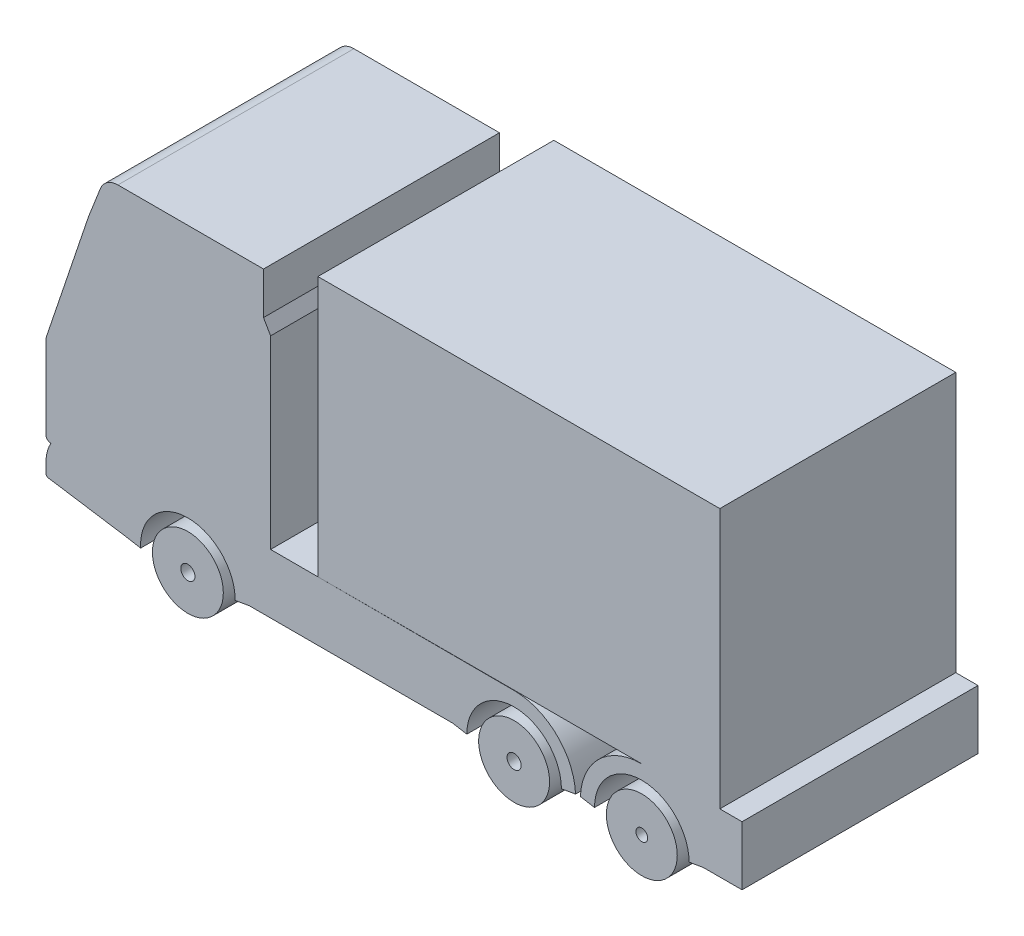
SolidWorks part; units mm, degrees
ref_plane "Front Plane" through (0, 0, 0) normal (0, 0, 1) x (1, 0, 0)
ref_plane "Top Plane" through (0, 0, 0) normal (0, 1, 0) x (1, 0, 0)
ref_plane "Right Plane" through (0, 0, 0) normal (1, 0, 0) x (0, 0, -1)
sketch "Sketch1" plane through (0, 0, 0) normal (0, 0, 1) x (1, 0, 0)
  line L0 (1512.2242, 1030.7259) -> (1489.9408, 1030.763)
  line L1 (0, 538.3532) -> (0, 642.5001)
  line L2 (6300, 1028.4561) -> (7360, 1028.4561)
  line L3 (7360, 404.413) -> (7360, 1028.4561)
  line L4 (7360, 1028.4561) -> (7125, 1028.4561)
  line L5 (4950, 1025) -> (2300, 1029.4138)
  line L6 (850, 380.8409) -> (25.403, 508.7075)
  line L7 (2300, 879.4865) -> (2375, 879.3595)
  line L8 (2149.6887, 400.9569) -> (1999.9605, 374.5558)
  line L9 (2300, 3091.147) -> (2300, 870.119)
  line L10 (0, 890) -> (50, 890)
  line L11 (2300, 3091.147) -> (2300, 3560)
  line L12 (760.69, 3560) -> (2300, 3560)
  line L13 (4450, 375) -> (4300.5185, 400.9569)
  line L14 (5450, 375) -> (5599.4815, 400.9569)
  line L15 (5800, 378.4561) -> (5650.5185, 404.413)
  line L16 (6800, 378.4561) -> (6949.4815, 404.413)
  line L17 (7360, 404.413) -> (6949.4815, 404.413)
  line L19 (6949.4815, 404.413) -> (7360, 404.413)
  line L20 (2300, 3115) -> (450, 3115)
  line L21 (1500, 880.8409) -> (1501.693, 880.838)
  line L22 (4300.5185, 400.9569) -> (2149.6887, 400.9569)
  line L24 (850, 380.8409) -> (1000.7067, 354.2672)
  line L25 (450, 3115) -> (572.7515, 3428.404)
  line L26 (8.1235, 1803.6692) -> (450, 3115)
  line L27 (50, 890) -> (0, 890)
  line L28 (0, 1754.9756) -> (0, 890)
  line L29 (2300, 3560) -> (2300, 3115)
  line L31 (2300, 3115) -> (2375, 2985.0962)
  line L34 (2300, 870.119) -> (2300, 400.9569)
  line L35 (0, 455.7477) -> (0, 642.5001)
  line L36 (2300, 400.9569) -> (2149.6887, 400.9569)
  line L37 (2375, 2985.0962) -> (2375, 1029.2889)
  line L38 (2375, 1029.2889) -> (2300, 1029.4138)
  line L39 (2300, 1029.4138) -> (2375, 954.1635)
  line L40 (2375, 954.1635) -> (2375, 400.9569)
  line L41 (2375, 400.9569) -> (2149.6887, 400.9569)
  line L43 (2875, 1028.4561) -> (7125, 1028.4561)
  line L44 (2875, 1028.4561) -> (2875, 3778.4561)
  line L45 (2875, 3778.4561) -> (7125, 3778.4561)
  line L46 (7125, 1028.4561) -> (7125, 3778.4561)
  circle A0 centre (1500, 380.8409) radius 375
  circle A1 centre (4950, 375) radius 375
  circle A2 centre (6300, 378.4561) radius 375
  arc A3 (1000.7067, 354.2672) -> (1999.9605, 374.5558) centre (1500, 380.8409) cw
  arc A4 (4450, 375) -> (5450, 375) centre (4950, 375) cw
  arc A5 (5800, 378.4561) -> (6800, 378.4561) centre (6300, 378.4561) cw
  arc A6 (850, 380.8409) -> (2149.6887, 400.9569) centre (1500, 380.8409) cw
  arc A7 (4300.5185, 400.9569) -> (5599.4815, 400.9569) centre (4950, 375) cw
  arc A8 (5650.5185, 404.413) -> (6949.4815, 404.413) centre (6300, 378.4561) cw
  circle A9 centre (1500, 380.8409) radius 75
  circle A10 centre (4950, 375) radius 250
  circle A11 centre (6300, 378.4561) radius 250
  circle A12 centre (1500, 380.8409) radius 250
  circle A13 centre (4950, 375) radius 75
  circle A14 centre (6300, 378.4561) radius 62.5
  arc A15 (1000, 380.8409) -> (2000, 380.8409) centre (1500, 380.8409) cw
  arc A16 (760.69, 3560) -> (572.7515, 3428.404) centre (760.69, 3360) ccw
  arc A17 (0, 538.3532) -> (25.403, 508.7075) centre (30, 538.3532) ccw
  arc A18 (0, 890) -> (52.1855, 840.0478) centre (50, 890) ccw
  arc A19 (8.1235, 1803.6692) -> (0, 1754.9756) centre (150, 1754.9756) ccw
  arc A20 (52.1855, 840.0478) -> (0, 642.5001) centre (400, 642.5001) ccw
  dimension "D6" = 750
  dimension "D7" = 500
  dimension "D8" = 500
  dimension "D9" = 500
  dimension "D10" = 650
  dimension "D11" = 650
  dimension "D12" = 650
  dimension "D13" = 500
  dimension "D2" = 150
  dimension "D14" = 150
  dimension "D15" = 500
  dimension "D16" = 125
  dimension "D17" = 500
  dimension "D22" = 750
  dimension "D23" = 750
  dimension "D26" = 200
  dimension "D28" = 2750
  dimension "D29" = 4250
  dimension "D21" = 30
  dimension "D27" = 150
  dimension "D4" = 30
  dimension "D5" = 650
  dimension "D3" = 500
  dimension "D25" = 445
extrude "Boss-Extrude1" add sketch "Sketch1" along normal blind 2495
